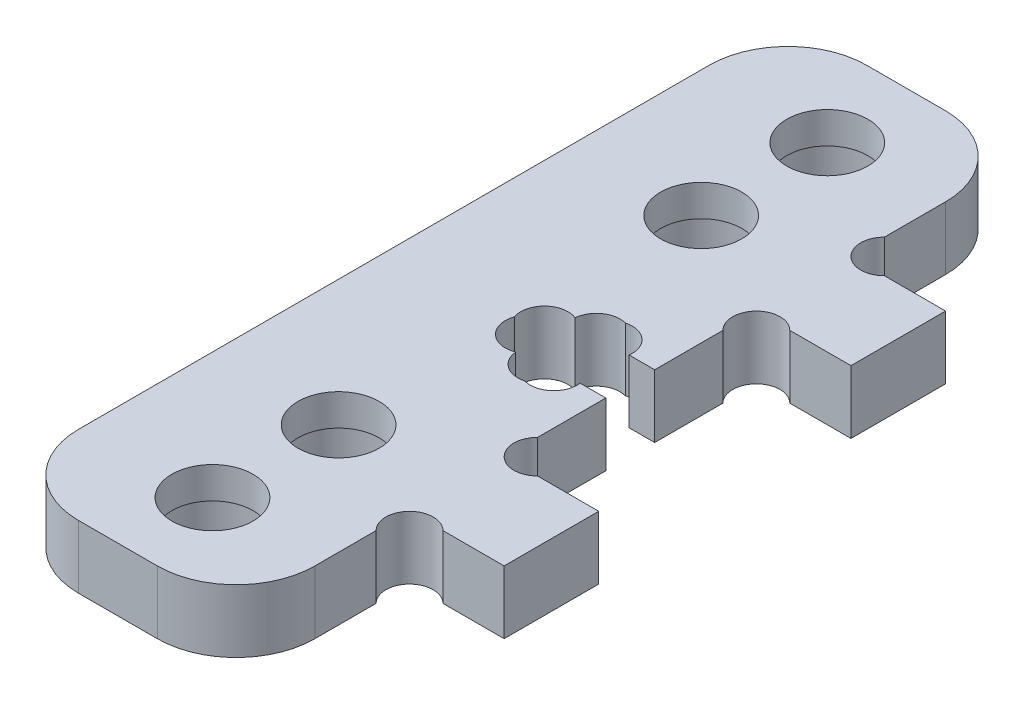
SolidWorks part; units mm, degrees
ref_plane "Alzado" through (0, 0, 0) normal (0, 0, 1) x (1, 0, 0)
ref_plane "Planta" through (0, 0, 0) normal (0, 1, 0) x (1, 0, 0)
ref_plane "Vista lateral" through (0, 0, 0) normal (1, 0, 0) x (0, 0, -1)
sketch "Croquis1" plane through (0, 0, 0) normal (0, 1, 0) x (1, 0, 0)
  line L0 (10.5, 14) -> (10.5, -14) construction
  line L1 (-2.5, -25) -> (2.5, -25)
  line L2 (-7.5, -20) -> (-7.5, 20)
  line L3 (-2.5, 25) -> (2.5, 25)
  line L4 (7.5, -20) -> (7.5, -14)
  line L5 (-7.5, -25) -> (7.5, 25) construction
  line L6 (-7.5, 25) -> (7.5, -25) construction
  line L7 (7.5, 14) -> (13.5, 14)
  line L8 (7.5, -8) -> (7.5, -1.55)
  line L9 (7.5, 8) -> (13.5, 8)
  line L10 (13.5, 14) -> (13.5, 8)
  line L11 (7.5, -8) -> (13.5, -8)
  line L12 (13.5, 11) -> (8.3263, 11) construction
  line L13 (7.5, -14) -> (13.5, -14)
  line L14 (13.5, -8) -> (13.5, -14)
  line L15 (0, 0) -> (10.5, 0) construction
  line L16 (7.5, 14) -> (7.5, 20)
  line L17 (5.45, -1.55) -> (5.45, -2.8)
  line L18 (2.55, 2.8) -> (5.45, 2.8)
  line L19 (2.55, 2.8) -> (2.55, 1.55)
  line L20 (2.55, -2.8) -> (5.45, -2.8)
  line L21 (5.45, 2.8) -> (5.45, 1.55)
  line L22 (0.5, 1.55) -> (2.55, 1.55)
  line L23 (0.5, 1.55) -> (0.5, -1.55)
  line L24 (0.5, -1.55) -> (2.55, -1.55)
  line L25 (7.5, 1.55) -> (7.5, 8)
  line L26 (5.45, 1.55) -> (7.5, 1.55)
  line L27 (2.55, -1.55) -> (2.55, -2.8)
  line L28 (5.45, -1.55) -> (7.5, -1.55)
  line L29 (0.5, 0) -> (0, 0) construction
  line L30 (4, 2.8) -> (4, -2.8) construction
  line L31 (4, 0) -> (0.5, 0) construction
  arc A0 (-2.5, -25) -> (-7.5, -20) centre (-2.5, -20) cw
  arc A1 (2.5, -25) -> (7.5, -20) centre (2.5, -20) ccw
  arc A2 (2.5, 25) -> (7.5, 20) centre (2.5, 20) cw
  arc A3 (-7.5, 20) -> (-2.5, 25) centre (-2.5, 20) cw
  point P0 (0, 0)
  dimension "D3" = 5
  dimension "D4" = 6
  dimension "D1" = 50
  dimension "D2" = 15
  dimension "D5" = 6
  dimension "D6" = 14
  dimension "D7" = 3.1
  dimension "D8" = 5.6
  dimension "D9" = 2.9
  dimension "D10" = 7
  dimension "D11" = 3.5
extrude "Saliente-Extruir1" add sketch "Croquis1" along normal blind 4
sketch "Croquis4" plane through (0, 0, 0) normal (0, 1, 0) x (1, 0, 0)
  line L1 (-7.125, 26.5) -> (-0.975, 26.5)
  line L2 (-7.125, 26.5) -> (-7.125, -26.5)
  line L3 (-7.125, -26.5) -> (-0.975, -26.5)
  line L4 (-0.975, 26.5) -> (-0.975, -26.5)
  line L6 (-4.05, 26.5) -> (-4.05, -26.5) construction
  line L7 (7.5, -20) -> (7.5, -14) construction
  line L8 (2.5, 25) -> (-2.5, 25) construction
  line L9 (-2.5, -25) -> (2.5, -25) construction
  dimension "D1" = 6.15
  dimension "D2" = 11.55
  dimension "D3" = 1.5
  dimension "D4" = 1.5
sketch "Croquis9" plane through (0, 4, 0) normal (0, 1, 0) x (1, 0, 0)
  line L24 (-2.5, -25) -> (2.5, -25)
  line L25 (7.5, -20) -> (7.5, -14)
  line L26 (7.5, -14) -> (13.5, -14)
  line L27 (13.5, -14) -> (13.5, -8)
  line L28 (13.5, -8) -> (7.5, -8)
  line L29 (7.5, -8) -> (7.5, -1.55)
  line L30 (7.5, -1.55) -> (5.45, -1.55)
  line L31 (5.45, -1.55) -> (5.45, -2.8)
  line L32 (5.45, -2.8) -> (2.55, -2.8)
  line L33 (2.55, -2.8) -> (2.55, -1.55)
  line L34 (2.55, -1.55) -> (0.5, -1.55)
  line L35 (0.5, -1.55) -> (0.5, 1.55)
  line L36 (0.5, 1.55) -> (2.55, 1.55)
  line L37 (2.55, 1.55) -> (2.55, 2.8)
  line L38 (2.55, 2.8) -> (5.45, 2.8)
  line L39 (5.45, 2.8) -> (5.45, 1.55)
  line L40 (5.45, 1.55) -> (7.5, 1.55)
  line L41 (7.5, 1.55) -> (7.5, 8)
  line L42 (7.5, 8) -> (13.5, 8)
  line L43 (13.5, 8) -> (13.5, 14)
  line L44 (13.5, 14) -> (7.5, 14)
  line L45 (7.5, 14) -> (7.5, 20)
  line L46 (2.5, 25) -> (-2.5, 25)
  line L47 (-7.5, 20) -> (-7.5, -20)
  line L48 (-2.5, -25) -> (2.5, -25)
  line L49 (7.5, -20) -> (7.5, -14)
  line L50 (7.5, -14) -> (13.5, -14)
  line L51 (13.5, -14) -> (13.5, -8)
  line L52 (13.5, -8) -> (7.5, -8)
  line L53 (7.5, -8) -> (7.5, -1.55)
  line L54 (7.5, -1.55) -> (5.45, -1.55)
  line L55 (5.45, -1.55) -> (5.45, -2.8)
  line L56 (5.45, -2.8) -> (2.55, -2.8)
  line L57 (2.55, -2.8) -> (2.55, -1.55)
  line L58 (2.55, -1.55) -> (0.5, -1.55)
  line L59 (0.5, -1.55) -> (0.5, 1.55)
  line L60 (0.5, 1.55) -> (2.55, 1.55)
  line L61 (2.55, 1.55) -> (2.55, 2.8)
  line L62 (2.55, 2.8) -> (5.45, 2.8)
  line L63 (5.45, 2.8) -> (5.45, 1.55)
  line L64 (5.45, 1.55) -> (7.5, 1.55)
  line L65 (7.5, 1.55) -> (7.5, 8)
  line L66 (7.5, 8) -> (13.5, 8)
  line L67 (13.5, 8) -> (13.5, 14)
  line L68 (13.5, 14) -> (7.5, 14)
  line L69 (7.5, 14) -> (7.5, 20)
  line L70 (2.5, 25) -> (-2.5, 25)
  line L71 (-7.5, 20) -> (-7.5, -20)
  arc A4 (-7.5, -20) -> (-2.5, -25) centre (-2.5, -20) ccw
  arc A5 (2.5, -25) -> (7.5, -20) centre (2.5, -20) ccw
  arc A6 (7.5, 20) -> (2.5, 25) centre (2.5, 20) ccw
  arc A7 (-2.5, 25) -> (-7.5, 20) centre (-2.5, 20) ccw
  arc A8 (-7.5, -20) -> (-2.5, -25) centre (-2.5, -20) ccw
  arc A9 (2.5, -25) -> (7.5, -20) centre (2.5, -20) ccw
  arc A10 (7.5, 20) -> (2.5, 25) centre (2.5, 20) ccw
  arc A11 (-2.5, 25) -> (-7.5, 20) centre (-2.5, 20) ccw
  dimension "D1" = 0
sketch "Croquis6" plane through (0, 4, 0) normal (0, 1, 0) x (1, 0, 0)
  line L0 (0.5, 1.55) -> (2.55, 1.55) construction
  line L1 (0.5, -1.55) -> (0.5, 1.55) construction
  line L2 (2.55, -1.55) -> (0.5, -1.55) construction
  line L3 (0.5, 1.55) -> (2, 0.05)
  line L4 (0.5, -1.55) -> (2, -0.05)
  line L5 (2.55, 2.8) -> (5.45, 2.8) construction
  line L6 (2.55, 1.55) -> (2.55, 2.8) construction
  line L7 (2.55, 2.8) -> (4.05, 1.3)
  line L8 (5.45, 2.8) -> (5.45, 1.55) construction
  line L9 (5.45, 2.8) -> (3.95, 1.3)
  line L10 (2.55, -2.8) -> (2.55, -1.55) construction
  line L11 (5.45, -2.8) -> (2.55, -2.8) construction
  line L12 (2.55, -2.8) -> (4.05, -1.3)
  line L13 (5.45, -1.55) -> (5.45, -2.8) construction
  line L14 (5.45, -2.8) -> (3.95, -1.3)
  circle A0 centre (2, 0.05) radius 1.5
  circle A1 centre (2, -0.05) radius 1.5
  circle A2 centre (4.05, -1.3) radius 1.5
  circle A3 centre (3.95, -1.3) radius 1.5
  circle A4 centre (3.95, 1.3) radius 1.5
  circle A5 centre (4.05, 1.3) radius 1.5
  dimension "D1" = 3
sketch "Croquis7" plane through (0, 4, 0) normal (0, 1, 0) x (1, 0, 0)
  line L0 (0.5, 1.55) -> (2, 0.05) construction
  line L1 (0.5, -1.55) -> (2, -0.05) construction
  line L2 (2.55, -2.8) -> (4.05, -1.3) construction
  line L3 (5.45, -2.8) -> (3.95, -1.3) construction
  line L4 (5.45, 2.8) -> (3.95, 1.3) construction
  line L5 (2.55, 2.8) -> (4.05, 1.3) construction
  line L11 (5.8773, 1.55) -> (7.5, 1.55)
  line L12 (7.5, 1.55) -> (7.5, -1.55)
  line L13 (7.5, -1.55) -> (5.8773, -1.55)
  arc A0 (2.1175, 1.8822) -> (0.1427, 0) centre (1.5607, 0.4893) ccw
  arc A1 (0.1427, 0) -> (2.1175, -1.8822) centre (1.5607, -0.4893) ccw
  arc A2 (2.1175, -1.8822) -> (4, -3.1879) centre (3.6107, -1.7393) ccw
  arc A3 (4, -3.1879) -> (5.8773, -1.55) centre (4.3893, -1.7393) ccw
  arc A4 (5.8773, 1.55) -> (4, 3.1879) centre (4.3893, 1.7393) ccw
  arc A5 (4, 3.1879) -> (2.1175, 1.8822) centre (3.6107, 1.7393) ccw
  dimension "D1" = 3
extrude "Cortar-Extruir4" cut sketch "Croquis7" against normal through all
sketch "Croquis10" plane through (0, 4, 0) normal (0, 1, 0) x (1, 0, 0)
  line L0 (0, 0) -> (23.8324, 0) construction
  line L1 (13.5, 14) -> (7.5, 14) construction
  line L2 (7.5, 14) -> (7.5, 20) construction
  line L3 (7.5, 8) -> (13.5, 8) construction
  line L4 (7.5, 1.55) -> (7.5, 8) construction
  line L5 (7.5, 14) -> (9, 15.5) construction
  line L7 (7.5, 8) -> (9, 6.5) construction
  circle A0 centre (9, 15.5) radius 1.5 construction
  circle A1 centre (9, 6.5) radius 1.5 construction
  circle A2 centre (8.5607, 15.0607) radius 1.5
  circle A3 centre (8.5607, 6.9393) radius 1.5
  circle A4 centre (8.5607, -15.0607) radius 1.5
  circle A5 centre (8.5607, -6.9393) radius 1.5
  dimension "D1" = 3
extrude "Cortar-Extruir5" cut sketch "Croquis10" against normal through all
sketch "Croquis12" plane through (0, 0, 0) normal (0, -1, 0) x (1, 0, 0)
  line L0 (2.5, -25) -> (-2.5, -25) construction
  line L1 (7.5, -1.55) -> (7.5, -5.8787) construction
  circle A0 centre (0.5, -11.5) radius 2.575
  circle A1 centre (0.5, -19.5) radius 2.575
  dimension "D1" = 5.15
  dimension "D2" = 8
  dimension "D3" = 5.5
  dimension "D4" = 7
extrude "Cortar-Extruir6" cut sketch "Croquis12" against normal through all
sketch "Croquis13" plane through (0, 0, 0) normal (0, -1, 0) x (1, 0, 0)
  circle A0 centre (0.5, -11.5) radius 3
  circle A1 centre (0.5, -19.5) radius 3
  dimension "D1" = 6
extrude "Cortar-Extruir7" cut sketch "Croquis13" against normal blind 2
mirror "Simetría1" about plane through (0, 0, 0) normal (0, 0, 1) of "Cortar-Extruir7", "Cortar-Extruir6"
